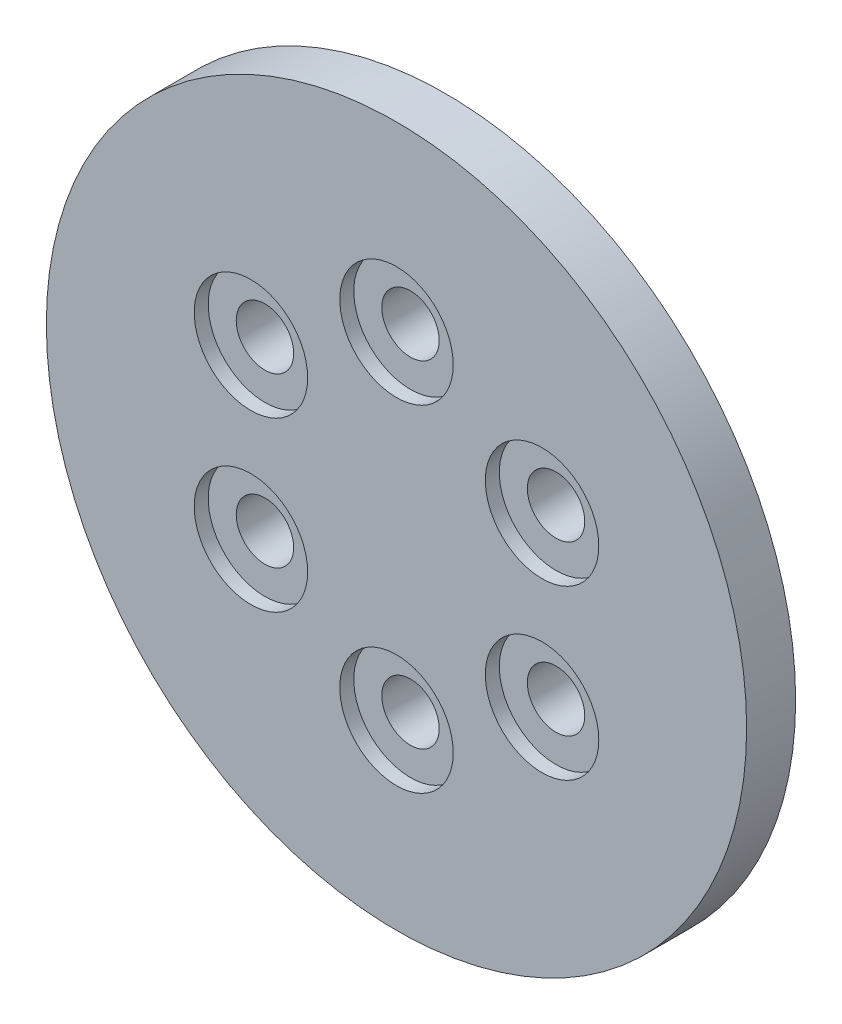
SolidWorks part; units mm, degrees
ref_plane "前视基准面" through (0, 0, 0) normal (0, 0, 1) x (1, 0, 0)
ref_plane "上视基准面" through (0, 0, 0) normal (0, 1, 0) x (1, 0, 0)
ref_plane "右视基准面" through (0, 0, 0) normal (1, 0, 0) x (0, 0, -1)
sketch "草图1" plane through (0, 0, 0) normal (0, 0, 1) x (1, 0, 0)
  circle A0 centre (0, 0) radius 25
  circle A1 centre (0, 0) radius 12 construction
  point P4 (0, 12)
  point P7 (10.3923, 6)
  point P8 (10.3923, -6)
  point P9 (0, -12)
  point P10 (-10.3923, -6)
  point P11 (-10.3923, 6)
  point P12 (0, 0)
  dimension "D1" = 50
  dimension "D2" = 24
  dimension "D3" = 6
extrude "凸台-拉伸1" add sketch "草图1" along normal blind 4
sketch "草图4" plane through (0, 0, 0) normal (0, 0, -1) x (-1, 0, 0)
  circle A0 centre (0, 0) radius 12 construction
  circle A1 centre (0, 0) radius 25
  circle A2 centre (0, 0) radius 25
  circle A3 centre (0, 0) radius 12 construction
  circle A4 centre (0, 12) radius 2.05
  circle A5 centre (10.3923, 6) radius 2.05
  circle A6 centre (10.3923, -6) radius 2.05
  circle A7 centre (0, -12) radius 2.05
  circle A8 centre (-10.3923, -6) radius 2.05
  circle A9 centre (-10.3923, 6) radius 2.05
  point P0 (10.3923, 6)
  point P1 (10.3923, -6)
  point P7 (0, -12)
  point P9 (-10.3923, -6)
  point P11 (-10.3923, 6)
  point P13 (0, 12)
  point P33 (0, 0)
  dimension "D2" = 4.1
  dimension "D1" = 0
  dimension "D3" = 6
extrude "切除-拉伸1" cut sketch "草图4" against normal blind 10 contours A8 | A9 | A4 | A5 | A6 | A7
sketch "草图5" plane through (0, 0, 4) normal (0, 0, 1) x (1, 0, 0)
  circle A0 centre (-10.3923, 6) radius 2.05 construction
  circle A1 centre (-10.3923, -6) radius 2.05 construction
  circle A2 centre (0, -12) radius 2.05 construction
  circle A3 centre (10.3923, -6) radius 2.05 construction
  circle A4 centre (10.3923, 6) radius 2.05 construction
  circle A5 centre (0, 12) radius 2.05 construction
  circle A6 centre (-10.3923, 6) radius 2.05
  circle A7 centre (-10.3923, -6) radius 2.05
  circle A8 centre (0, -12) radius 2.05
  circle A9 centre (10.3923, -6) radius 2.05
  circle A10 centre (10.3923, 6) radius 2.05
  circle A11 centre (0, 12) radius 2.05
  circle A12 centre (-10.3923, 6) radius 4.05
  circle A13 centre (-10.3923, -6) radius 4.05
  circle A14 centre (0, -12) radius 4.05
  circle A15 centre (10.3923, -6) radius 4.05
  circle A16 centre (10.3923, 6) radius 4.05
  circle A17 centre (0, 12) radius 4.05
  dimension "D1" = 2
extrude "切除-拉伸2" cut sketch "草图5" against normal blind 1
sketch "草图6" plane through (0, 0, 0) normal (0, 0, -1) x (-1, 0, 0)
  circle A0 centre (0, 0) radius 20
  circle A1 centre (0, 0) radius 25
  circle A2 centre (0, 0) radius 25
  dimension "D1" = 0
  dimension "D2" = 5
extrude "切除-拉伸3" cut sketch "草图6" against normal blind 0.5
